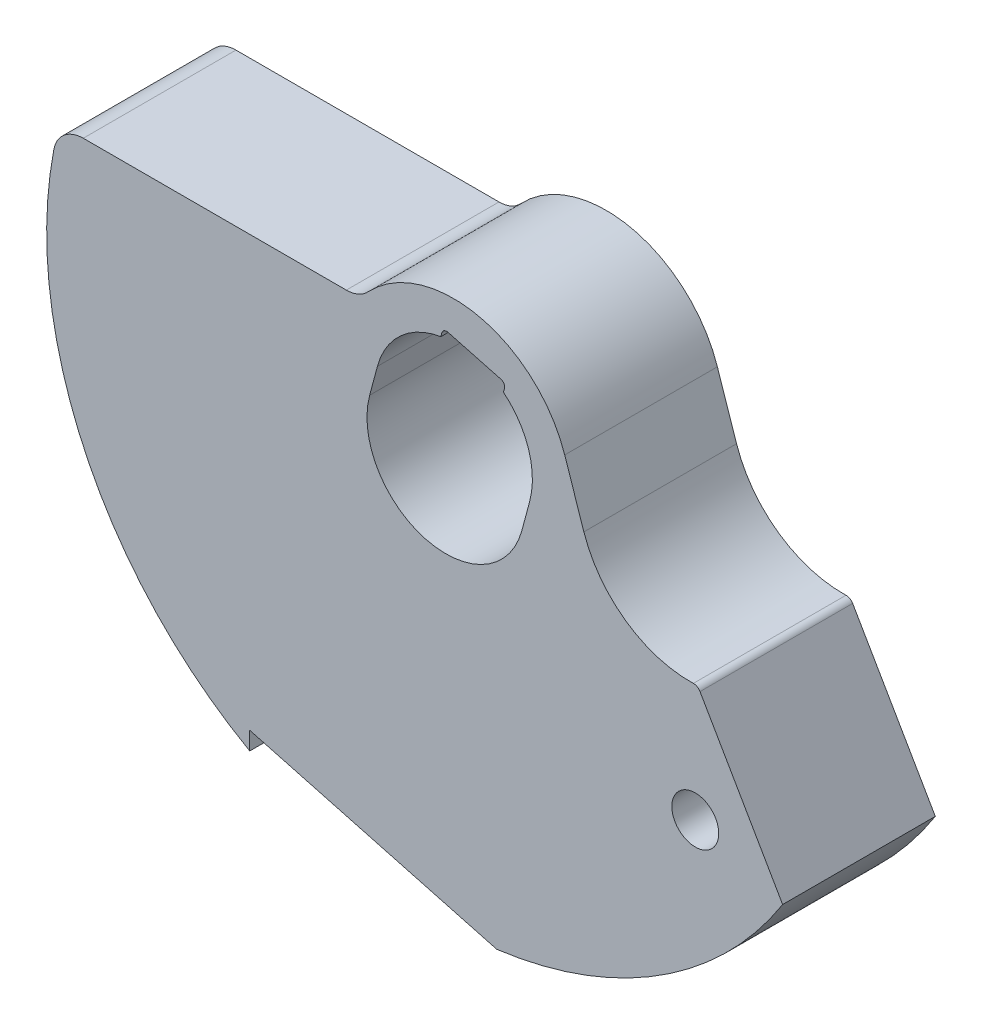
SolidWorks part; units mm, degrees
ref_plane "Front Plane" through (0, 0, 0) normal (0, 0, 1) x (1, 0, 0)
ref_plane "Top Plane" through (0, 0, 0) normal (0, 1, 0) x (1, 0, 0)
ref_plane "Right Plane" through (0, 0, 0) normal (1, 0, 0) x (0, 0, -1)
sketch "Sketch1" plane through (0, 0, 0) normal (0, 0, 1) x (1, 0, 0)
  line L0 (0, 40.7088) -> (0, -42.4788) construction
  line L1 (50.0011, 0) -> (-47.9361, 0) construction
  line L2 (0, 0) -> (4.815, 17.9697) construction
  line L3 (-7.4706, 2.0017) -> (6.4814, -1.7367) construction
  line L4 (-7.0762, 3.4738) -> (6.8758, -0.2646) construction
  line L5 (-3.8765, 1.0387) -> (-3.482, 2.5108)
  line L6 (4.2709, 0.4334) -> (3.8765, -1.0387)
  line L7 (-5.0653, 5.08) -> (-18.4566, 5.08)
  line L8 (6.0531, 3.3717) -> (7.0281, 0.4672)
  line L9 (12.9403, -3.6173) -> (17.147, -10.9034)
  line L10 (0, 0) -> (5.8427, -10.1199) construction
  line L11 (0, 0) -> (43.883, -11.7584) construction
  line L12 (12.7, 40.7088) -> (12.7, -42.4788) construction
  line L13 (50.0011, -9.398) -> (-47.9361, -9.398) construction
  line L14 (-1.0387, -3.8765) -> (-9.0244, -1.7367) construction
  line L15 (-9.9822, -16.7843) -> (-9.9822, -17.6991)
  line L16 (-9.9822, -16.7843) -> (2.5931, -20.1539)
  line L17 (2.8088, 5.0851) -> (0.11, 5.8082)
  line L18 (1.4594, 5.4467) -> (-6.5263, 7.5864) construction
  line L21 (2.9359, 4.578) -> (2.9884, 4.774)
  line L24 (-0.2536, 5.4326) -> (-0.2011, 5.6286)
  arc A0 (-3.8765, 1.0387) -> (3.8765, -1.0387) centre (0, 0) ccw
  arc A1 (6.1601, -0.0728) -> (6.1791, 0) centre (0.3944, 1.4721) ccw
  arc A2 (4.2709, 0.4334) -> (2.9359, 4.578) centre (0.3944, 1.4721) ccw
  arc A3 (7.0281, 0.4672) -> (12.6001, -3.4269) centre (12.446, 2.286) ccw
  arc A4 (6.0531, 3.3717) -> (-3.9548, 5.5602) centre (0.3944, 1.4721) ccw
  arc A5 (-19.953, 3.8443) -> (-9.9822, -17.6991) centre (0, 0) ccw
  arc A6 (12.6001, -3.4269) -> (12.9403, -3.6173) centre (12.6104, -3.8078) cw
  arc A7 (2.5931, -20.1539) -> (17.147, -10.9034) centre (0, 0) ccw
  arc A8 (-18.4566, 5.08) -> (-19.953, 3.8443) centre (-18.4566, 3.556) ccw
  arc A9 (-5.0653, 5.08) -> (-3.9548, 5.5602) centre (-5.0653, 6.604) ccw
  circle A10 centre (12.7, -9.398) radius 1.1938
  arc A11 (-0.2536, 5.4326) -> (-3.482, 2.5108) centre (0.3944, 1.4721) ccw
  arc A12 (2.8088, 5.0851) -> (2.9884, 4.774) centre (2.7431, 4.8397) cw
  arc A13 (-0.2011, 5.6286) -> (0.11, 5.8082) centre (0.0443, 5.5629) cw
  point P35 (-9.9822, 40.7088)
  point P36 (-9.9822, -42.4788)
  point P48 (1.5947, -0.4273)
  point P50 (6.4097, 17.5424)
  point P51 (-1.5947, 0.4273)
  point P52 (3.2202, 18.397)
  dimension "D1" = 8.0264
  dimension "D4" = 11.938
  dimension "D6" = 11.43
  dimension "D11" = 40.64
  dimension "D12" = 0.381
  dimension "D16" = 1.524
  dimension "D17" = 1.524
  dimension "D20" = 2.3876
  dimension "D24" = 0.254
  dimension "D2" = 15
  dimension "D5" = 5.08
  dimension "D7" = 2.286
  dimension "D8" = 12.446
  dimension "D9" = 60
  dimension "D10" = 9.398
  dimension "D13" = 15
  dimension "D14" = 18.796
  dimension "D15" = 9.9822
  dimension "D22" = 3.302
  dimension "D23" = 1.651
  dimension "D3" = 1.524
  dimension "D18" = 12.7
  dimension "D19" = 9.398
  dimension "D21" = 9.652
extrude "Boss-Extrude1" add sketch "Sketch1" against normal blind 7.7724
